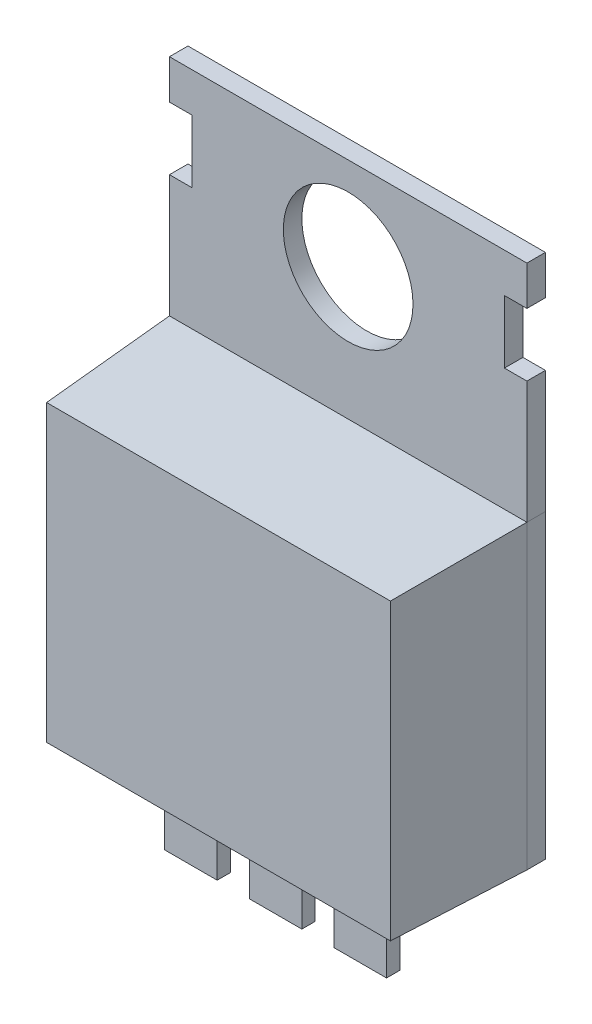
SolidWorks part; units mm, degrees
ref_plane "Front Plane" through (0, 0, 0) normal (0, 0, 1) x (1, 0, 0)
ref_plane "Top Plane" through (0, 0, 0) normal (0, 1, 0) x (1, 0, 0)
ref_plane "Right Plane" through (0, 0, 0) normal (1, 0, 0) x (0, 0, -1)
sketch "Sketch1" plane through (0, 0, 0) normal (0, 1, 0) x (1, 0, 0)
  line L1 (-4.825, -2) -> (4.825, -2)
  line L2 (-4.825, -2) -> (-4.825, 2)
  line L3 (-4.825, 2) -> (4.825, 2)
  line L4 (4.825, -2) -> (4.825, 2)
  line L5 (-4.825, -2) -> (4.825, 2) construction
  line L6 (-4.825, 2) -> (4.825, -2) construction
  point P0 (0, 0)
  dimension "D1" = 4
  dimension "D2" = 9.65
extrude "Boss-Extrude1" add sketch "Sketch1" along normal blind 8.13
chamfer "Chamfer2" distance 3.5 angle 3 1 edges at (0, 8.13, 2)
sketch "Sketch4" plane through (0, 8.13, 0) normal (0, 1, 0) x (1, 0, 0)
  line L1 (4.825, 2) -> (-4.825, 2)
  line L2 (4.825, 2) -> (4.825, 1.5)
  line L3 (4.825, 1.5) -> (-4.825, 1.5)
  line L4 (-4.825, 2) -> (-4.825, 1.5)
extrude "Boss-Extrude2" add sketch "Sketch4" along normal blind 6.06 separate body
chamfer "Chamfer3" distance 3.5 angle 3 1 edges at (4.825, 3.9733, 2)
chamfer "Chamfer4" distance 3.5 angle 3 1 edges at (-4.825, 3.9733, 2)
sketch "Sketch5" plane through (0, 0, -2) normal (0, 0, -1) x (-1, 0, 0)
  line L0 (-4.825, 8.13) -> (4.825, 8.13) construction
  line L1 (-3.795, 8.13) -> (3.795, 8.13)
  line L2 (-3.795, 8.13) -> (-3.795, 2.69)
  line L3 (-3.795, 2.69) -> (3.795, 2.69)
  line L4 (3.795, 8.13) -> (3.795, 2.69)
  line L5 (0, 8.13) -> (0, 2.69) construction
  line L6 (-4.825, 8.13) -> (-4.825, 0) construction
  line L7 (-4.825, 14.19) -> (4.825, 14.19) construction
  dimension "D1" = 7.59
  dimension "D2" = 4.825
  dimension "D3" = 11.5
extrude "Cut-Extrude1" cut sketch "Sketch5" against normal blind 0.5
sketch "Sketch7" plane through (0, 0, -1.5) normal (0, 0, -1) x (-1, 0, 0)
  line L1 (-3.795, 8.13) -> (3.795, 8.13)
  line L2 (-3.795, 8.13) -> (-3.795, 2.69)
  line L3 (-3.795, 2.69) -> (3.795, 2.69)
  line L4 (3.795, 8.13) -> (3.795, 2.69)
extrude "Boss-Extrude3" add sketch "Sketch7" along normal blind 0.5 separate body
sketch "Sketch8" plane through (0, 0, 0) normal (0, -1, 0) x (1, 0, 0)
  line L0 (4.825, -2) -> (-4.825, -2) construction
  line L1 (0.71, 0.1) -> (-0.71, 0.1)
  line L2 (0.71, 0.1) -> (0.71, 0.46)
  line L3 (0.71, 0.46) -> (-0.71, 0.46)
  line L4 (-0.71, 0.1) -> (-0.71, 0.46)
  line L5 (0, 0.1) -> (0, 0.46) construction
  line L6 (-4.825, -2) -> (-4.825, -1.5) construction
  line L7 (2.996, 0.1) -> (2.996, 0.46)
  line L8 (2.996, 0.1) -> (1.576, 0.1)
  line L9 (1.576, 0.1) -> (1.576, 0.46)
  line L10 (2.996, 0.46) -> (1.576, 0.46)
  line L11 (-1.576, 0.1) -> (-1.576, 0.46)
  line L12 (-1.576, 0.1) -> (-2.996, 0.1)
  line L13 (-2.996, 0.1) -> (-2.996, 0.46)
  line L14 (-1.576, 0.46) -> (-2.996, 0.46)
  dimension "D1" = 1.42
  dimension "D2" = 0.36
  dimension "D3" = 2.1
  dimension "D4" = 4.825
  dimension "D5" = 2
  dimension "D6" = 2
extrude "Boss-Extrude4" add sketch "Sketch8" along normal blind 2.46 separate body
sketch "Sketch9" plane through (0, 0, -1.5) normal (0, 0, 1) x (1, 0, 0)
  line L0 (-4.825, 14.19) -> (4.825, 14.19) construction
  circle A0 centre (0, 11.69) radius 1.75
  dimension "D1" = 2.5
extrude "Cut-Extrude2" cut sketch "Sketch9" against normal blind 2.46
sketch "Sketch10" plane through (0, 0, -1.5) normal (0, 0, 1) x (1, 0, 0)
  line L0 (0, 14.19) -> (0, 8.13) construction
  line L1 (-4.825, 14.19) -> (4.825, 14.19) construction
  line L2 (-3.795, 8.13) -> (3.795, 8.13) construction
  line L3 (-4.825, 14.19) -> (-4.825, 8.13) construction
  line L4 (-4.825, 13.1285) -> (-4.2188, 13.1285)
  line L5 (-4.825, 13.1285) -> (-4.825, 11.4314)
  line L6 (-4.825, 11.4314) -> (-4.2188, 11.4314)
  line L7 (-4.2188, 13.1285) -> (-4.2188, 11.4314)
  line L8 (4.825, 11.4314) -> (4.2188, 11.4314)
  line L9 (4.2188, 13.1285) -> (4.2188, 11.4314)
  line L10 (4.825, 13.1285) -> (4.2188, 13.1285)
  line L11 (4.825, 13.1285) -> (4.825, 11.4314)
extrude "Cut-Extrude3" cut sketch "Sketch10" against normal blind 2.46
